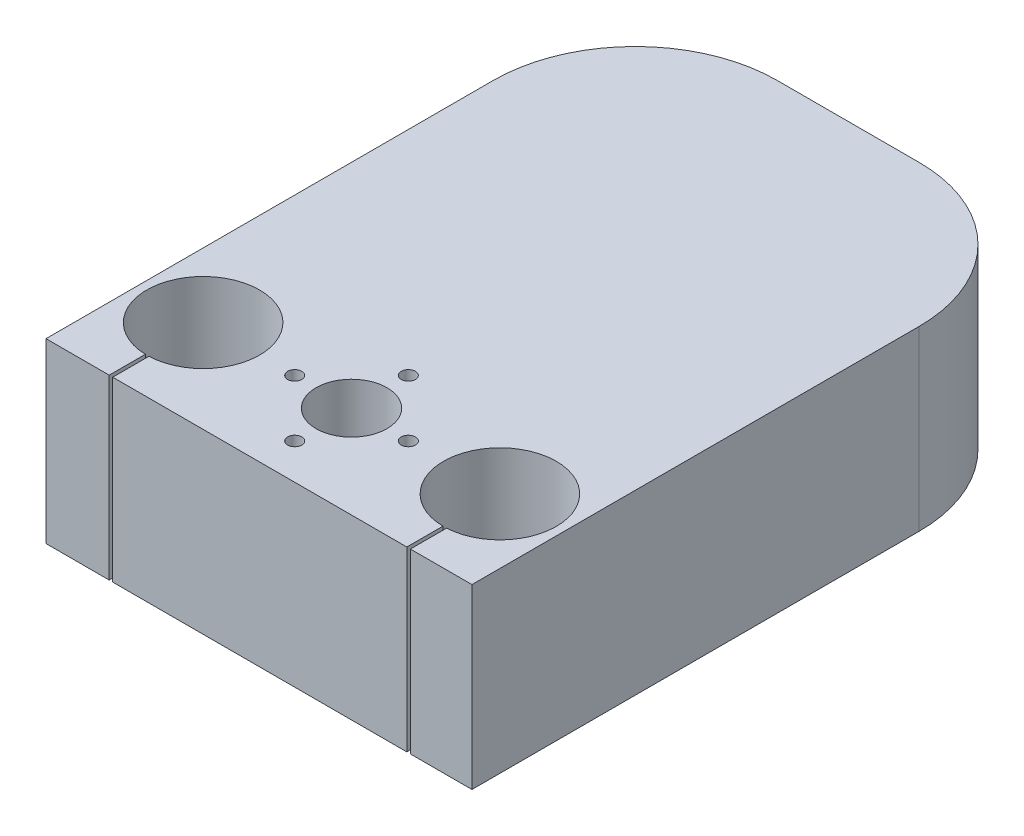
SolidWorks part; units mm, degrees
ref_plane "Front Plane" through (0, 0, 0) normal (0, 0, 1) x (1, 0, 0)
ref_plane "Top Plane" through (0, 0, 0) normal (0, 1, 0) x (1, 0, 0)
ref_plane "Right Plane" through (0, 0, 0) normal (1, 0, 0) x (0, 0, -1)
sketch "Sketch1" plane through (0, 0, 0) normal (0, 1, 0) x (1, 0, 0)
  line L1 (-30, 40) -> (30, 40)
  line L2 (-30, 40) -> (-30, -40)
  line L3 (-30, -40) -> (30, -40)
  line L4 (30, 40) -> (30, -40)
  line L5 (-30, 40) -> (30, -40) construction
  line L6 (-30, -40) -> (30, 40) construction
  point P0 (0, 0)
  dimension "D1" = 80
  dimension "D2" = 60
extrude "Boss-Extrude1" add sketch "Sketch1" along normal blind 25
fillet "Fillet1" radius 20 2 edges at (-30, 12.5, -40) (30, 12.5, -40)
sketch "Sketch3" plane through (0, 25, 0) normal (0, 1, 0) x (1, 0, 0)
  line L0 (-20.9, -13.0649) -> (-20.9, -46.8649) construction
  line L1 (20.9, -46.8649) -> (20.9, -13.0649) construction
  circle A0 centre (-20.9, -29.9649) radius 7.95
  circle A1 centre (20.9, -29.9649) radius 7.95
  dimension "D1" = 15.9
  dimension "D2" = 15.9
extrude "Cut-Extrude2" cut sketch "Sketch3" against normal blind 35
sketch "Sketch5" plane through (0, 0, 40) normal (0, 0, 1) x (1, 0, 0)
  line L1 (-30, 25) -> (30, 25)
  line L2 (-30, 25) -> (-30, 0)
  line L3 (-30, 0) -> (30, 0)
  line L4 (30, 25) -> (30, 0)
extrude "Boss-Extrude2" add sketch "Sketch5" along normal blind 3
sketch "Sketch6" plane through (0, 25, 0) normal (0, 1, 0) x (1, 0, 0)
  circle A0 centre (0, -29.9649) radius 5
  circle A1 centre (0, -37.9649) radius 1
  circle A2 centre (8, -29.9649) radius 1
  circle A3 centre (0, -21.9649) radius 1
  circle A4 centre (-8, -29.9649) radius 1
  dimension "D1" = 2
  dimension "D2" = 2
  dimension "D3" = 2
  dimension "D4" = 2
extrude "Cut-Extrude3" cut sketch "Sketch6" against normal through all
sketch "Sketch7" plane through (0, 0, 0) normal (0, -1, 0) x (-1, 0, 0)
  circle A0 centre (-0.2614, 23.5193) radius 2.5
  dimension "D1" = 5
extrude "Cut-Extrude4" cut sketch "Sketch7" against normal blind 15
sketch "Sketch8" plane through (0, 0, 0) normal (0, -1, 0) x (1, 0, 0)
  line L1 (21.3281, 36.9284) -> (20.8281, 36.9284)
  line L2 (21.3281, 36.9284) -> (21.3281, 44.459)
  line L3 (21.3281, 44.459) -> (20.8281, 44.459)
  line L4 (20.8281, 36.9284) -> (20.8281, 44.459)
  line L5 (-20.5987, 36.9284) -> (-21.0987, 36.9284)
  line L6 (-20.5987, 36.9284) -> (-20.5987, 44.459)
  line L7 (-20.5987, 44.459) -> (-21.0987, 44.459)
  line L8 (-21.0987, 36.9284) -> (-21.0987, 44.459)
  circle M14 centre (20.9, 29.9649) radius 7.95
  line M20 (30, 43) -> (-30, 43)
  dimension "D1" = 0.5
  dimension "D2" = 0.5
extrude "Cut-Extrude5" cut sketch "Sketch8" against normal through all contours L4 L2 M14 M20 | L4 L2 L3 M20 | L4 L1 L2 M14 | L6 L5 L8 L7
